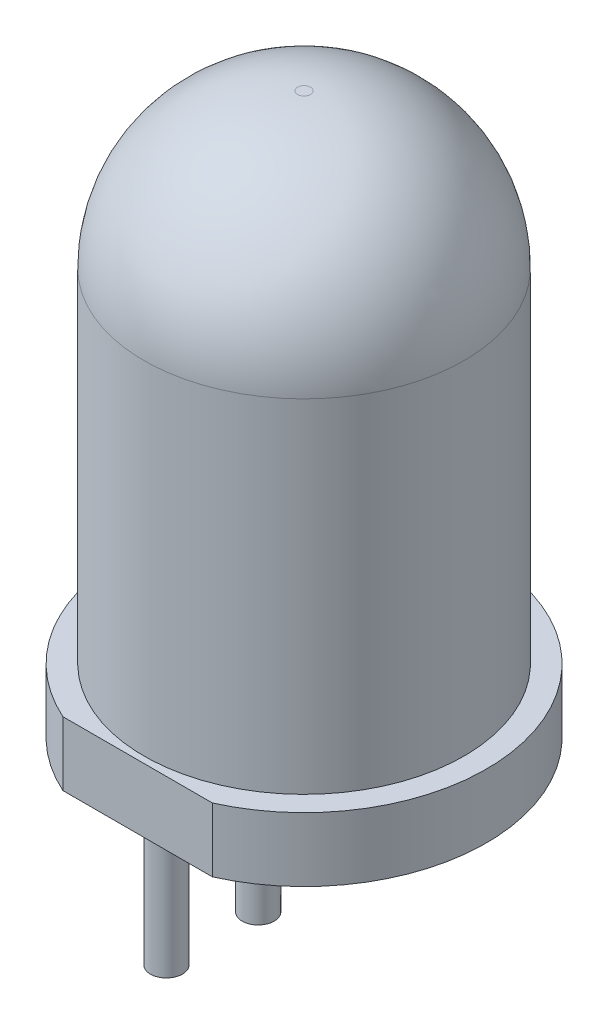
SolidWorks part; units mm, degrees
material "Perspex (TM) GS Acrylic Cast Sheet"
ref_plane "Front Plane" through (0, 0, 0) normal (0, 0, 1) x (1, 0, 0)
ref_plane "Top Plane" through (0, 0, 0) normal (0, 1, 0) x (1, 0, 0)
ref_plane "Right Plane" through (0, 0, 0) normal (1, 0, 0) x (0, 0, -1)
sketch "Sketch1" plane through (0, 0, 0) normal (0, 0, 1) x (1, 0, 0)
  line L0 (0, 0) -> (0, 8.75)
  line L1 (0, 0) -> (2.85, 0)
  line L2 (2.85, 0) -> (2.85, 1)
  line L3 (2.85, 1) -> (2.5, 1)
  line L4 (2.5, 1) -> (2.5, 6.35)
  line L5 (0, 8.75) -> (0.1, 8.75)
  arc A0 (2.5, 6.35) -> (0.1, 8.75) centre (0.1, 6.35) ccw
  dimension "D5" = 0.1
  dimension "D1" = 8.75
  dimension "D2" = 2.85
  dimension "D3" = 2.5
  dimension "D4" = 1
revolve "Revolve1" add sketch "Sketch1" angle 360 about L0
sketch "Sketch2" plane through (0, 0, 0) normal (0, -1, 0) x (1, 0, 0)
  line L0 (0, 0) -> (0, 2.6) construction
  line L1 (-1.1673, 2.6) -> (1.1673, 2.6)
  line L2 (0, 2.6) -> (0, 2.85) construction
  line L3 (0, 0) -> (0, -2.85) construction
  circle A0 centre (0, 0) radius 2.85 construction
  arc A1 (1.1673, 2.6) -> (-1.1673, 2.6) centre (0, 0) ccw
  dimension "D1" = 5.45
extrude "Cut-Extrude1" cut sketch "Sketch2" against normal up to surface (1 mm away) up to face at (0, 1, -2.5)
sketch "Sketch3" plane through (0, 0, 0) normal (0, -1, 0) x (1, 0, 0)
  line L0 (0, 0.7167) -> (0, -0.7167) construction
  line L1 (0, 0.7167) -> (0, 2.15) construction
  line L3 (0, -0.7167) -> (0, -2.15) construction
  circle A0 centre (0, -2.15) radius 0.25
  circle A1 centre (0, 2.15) radius 0.25
  circle A2 centre (0, -0.7167) radius 0.25
  circle A3 centre (0, 0.7167) radius 0.25
  dimension "D2" = 0.5
  dimension "D1" = 4.3
extrude "Boss-Extrude1" add sketch "Sketch3" along normal blind 2
